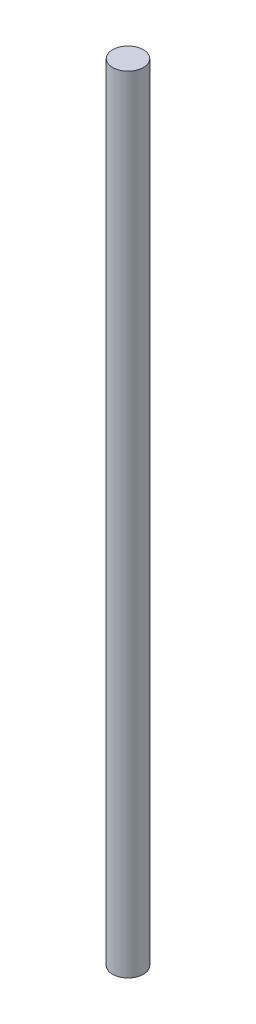
SolidWorks part; units mm, degrees
material "Acrylic (Medium-high impact)"
ref_plane "Front Plane" through (0, 0, 0) normal (0, 0, 1) x (1, 0, 0)
ref_plane "Top Plane" through (0, 0, 0) normal (0, 1, 0) x (1, 0, 0)
ref_plane "Right Plane" through (0, 0, 0) normal (1, 0, 0) x (0, 0, -1)
sketch "Sketch1" plane through (0, 0, 0) normal (0, 1, 0) x (1, 0, 0)
  circle A0 centre (0, 0) radius 3.175
  dimension "D1" = 6.35
extrude "Boss-Extrude1" add sketch "Sketch1" along normal blind 161.925
hole_wizard "#32 (0.116) Diameter Hole2" positions "Sketch4" profile "Sketch5" hole size "#32" standard "ANSI Inch"
sketch "Sketch4" plane through (0, 0, 0) normal (0, -1, 0) x (-1, 0, 0)
  point P0 (0, 0)
sketch "Sketch5" plane through (0, 0, 0) normal (1, 0, 0) x (0, 0, -1)
  line L0 (0, 0) -> (0, 4.5428)
  line L1 (0, 4.5428) -> (1.4732, 3.6576)
  line L2 (1.4732, 3.6576) -> (1.4732, 0)
  line L5 (1.4732, 0) -> (0, 0)
  line L10 (0, 4.5428) -> (-1.4732, 3.6576) construction
  line L11 (0, -6.35) -> (0, 107.95) construction
  dimension "Hole Dia." = 2.9464
  dimension "Hole Depth" = 3.6576
  dimension "Drill Angle" = 118
